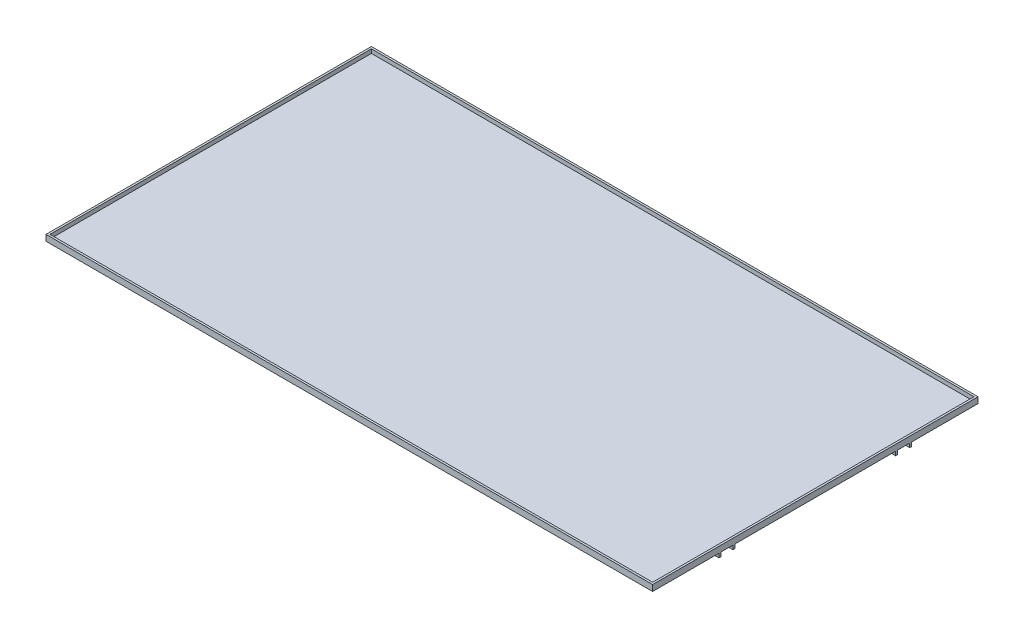
SolidWorks part; units mm, degrees
material "Plain Carbon Steel"
ref_plane "Front Plane" through (0, 0, 0) normal (0, 0, 1) x (1, 0, 0)
ref_plane "Top Plane" through (0, 0, 0) normal (0, 1, 0) x (1, 0, 0)
ref_plane "Right Plane" through (0, 0, 0) normal (1, 0, 0) x (0, 0, -1)
sketch "Sketch2" plane through (0, 0, 0) normal (0, 1, 0) x (1, 0, 0)
  line L1 (-750, 400) -> (750, 400)
  line L2 (-750, 400) -> (-750, -400)
  line L3 (-750, -400) -> (750, -400)
  line L4 (750, 400) -> (750, -400)
  line L5 (-750, 400) -> (750, -400) construction
  line L6 (-750, -400) -> (750, 400) construction
  line L7 (-755, 405) -> (755, 405)
  line L8 (-755, 405) -> (-755, -405)
  line L9 (-755, -405) -> (755, -405)
  line L10 (755, 405) -> (755, -405)
  line L11 (-755, 405) -> (755, -405) construction
  line L12 (-755, -405) -> (755, 405) construction
  point P0 (0, 0)
  point P6 (0, 0)
  dimension "D1" = 1500
  dimension "D2" = 800
  dimension "D3" = 1510
  dimension "D4" = 810
extrude "Boss-Extrude1" add sketch "Sketch2" along normal blind 10
sketch "Sketch3" plane through (0, 0, 0) normal (0, 1, 0) x (1, 0, 0)
  line L0 (-755, 405) -> (-755, -405) construction
  line L1 (755, -405) -> (-755, -405)
  line L2 (755, -405) -> (755, 405)
  line L3 (755, 405) -> (-755, 405)
  line L4 (-755, -405) -> (-755, 405)
  line L5 (755, -405) -> (-755, 405) construction
  line L6 (755, 405) -> (-755, -405) construction
  line L7 (755, 405) -> (-755, 405) construction
  line L8 (-750, 400) -> (-750, -400) construction
  line L9 (730, -380) -> (-730, -380)
  line L10 (730, -380) -> (730, -240)
  line L11 (730, 380) -> (-730, 380)
  line L12 (-730, -380) -> (-730, -240)
  line L13 (730, -380) -> (-730, 380) construction
  line L14 (730, 380) -> (-730, -380) construction
  line L15 (-750, -400) -> (750, -400) construction
  line L16 (-730, -240) -> (730, -240)
  line L17 (-730, -200) -> (-700, -200)
  line L18 (-730, 240) -> (730, 240)
  line L19 (-730, 200) -> (-700, 200)
  line L20 (-730, 240) -> (-730, 380)
  line L21 (-730, -200) -> (-730, 200)
  line L22 (730, -200) -> (730, 200)
  line L23 (730, 240) -> (730, 380)
  line L24 (0, 0) -> (-650, 0) construction
  line L25 (0, 0) -> (650, 0) construction
  line L26 (-500, 240) -> (-500, -240) construction
  line L27 (650, 240) -> (650, -240) construction
  line L28 (-600, 200) -> (600, 200)
  line L30 (-600, 200) -> (-600, -200)
  line L32 (-700, 200) -> (-700, -200)
  line L33 (-600, 200) -> (-700, -200) construction
  line L34 (-600, -200) -> (-700, 200) construction
  line L36 (600, 200) -> (600, -200)
  line L38 (700, 200) -> (700, -200)
  line L39 (600, 200) -> (700, -200) construction
  line L40 (600, -200) -> (700, 200) construction
  line L41 (-600, -200) -> (600, -200)
  line L42 (700, -200) -> (730, -200)
  line L43 (700, 200) -> (730, 200)
  point P0 (0, 0)
  point P10 (0, 0)
  dimension "D1" = 20
  dimension "D2" = 40
  dimension "20" = 20
  dimension "D3" = 40
  dimension "D4" = 200
  dimension "D5" = 200
  dimension "D6" = 650
  dimension "D7" = 650
  dimension "D8" = 100
  dimension "D9" = 100
extrude "Boss-Extrude2" add sketch "Sketch3" against normal blind 5
sketch "Sketch5" plane through (0, -5, 0) normal (0, -1, 0) x (1, 0, 0)
  line L0 (-755, 240) -> (755, 240)
  line L1 (-755, -405) -> (-755, 405) construction
  line L2 (755, 405) -> (755, -405) construction
  line L3 (755, 240) -> (755, 235)
  line L4 (755, 235) -> (-755, 235)
  line L5 (-755, 235) -> (-755, 240)
  dimension "D1" = 5
extrude "Boss-Extrude3" add sketch "Sketch5" along normal blind 10
pattern_linear "LPattern1" count 2 spacing 35 along (0, 0, -1) of "Boss-Extrude3"
pattern_linear "LPattern2" count 2 spacing 440 along (0, 0, -1) of "LPattern1", "Boss-Extrude3"
ref_plane "Plane1" through (0, 0, 220) normal (0, 0, 1) x (1, 0, 0)
sketch "Sketch6" plane through (0, 0, 220) normal (0, 0, 1) x (1, 0, 0)
  line L0 (630, -5) -> (630, -35)
  line L1 (-755, -5) -> (755, -5) construction
  line L3 (670, -35) -> (670, -5)
  line L4 (670, -5) -> (630, -5)
  line L5 (600, -5) -> (600, 0) construction
  arc A0 (670, -35) -> (630, -35) centre (650, -35) cw
  circle A1 centre (650, -35) radius 10
  dimension "D4" = 20
  dimension "D1" = 30
  dimension "D2" = 40
  dimension "30" = 30
extrude "Boss-Extrude4" add sketch "Sketch6" along normal mid plane 10
pattern_linear "LPattern3" count 2 spacing 440 along (0, 0, -1) of "Boss-Extrude4"
sketch "Sketch8" plane through (-755, 0, 0) normal (-1, 0, 0) x (0, 0, 1)
  line L0 (-200, -5) -> (200, -5) construction
  line L1 (-25, -35) -> (-25, -5)
  line L4 (25, -5) -> (25, -35)
  line L5 (-25, -5) -> (25, -5)
  circle A0 centre (0, -35) radius 10
  arc A1 (-25, -35) -> (25, -35) centre (0, -35) ccw
  dimension "D1" = 20
  dimension "D3" = 50
  dimension "D2" = 30
extrude "Boss-Extrude5" add sketch "Sketch8" against normal up to surface (25 mm away) up to face at (-730, -2.5, 0)
sketch "Sketch9" plane through (0, 0, 0) normal (0, 1, 0) x (1, 0, 0)
  line L0 (600, 200) -> (-600, 200) construction
  line L1 (280, 200) -> (200, 200)
  line L2 (280, 200) -> (280, -200)
  line L3 (280, -200) -> (200, -200)
  line L4 (200, 200) -> (200, -200)
  line L5 (-600, -200) -> (600, -200) construction
  line L6 (-600, 200) -> (-600, -200) construction
  dimension "D1" = 800
  dimension "D2" = 80
extrude "Boss-Extrude6" add sketch "Sketch9" against normal up to surface (5 mm away) up to face at (0, -5, -220)
ref_plane "Plane2" through (240, 0, 0) normal (-1, 0, 0) x (0, 0, 1)
sketch "Sketch10" plane through (240, 0, 0) normal (-1, 0, 0) x (0, 0, 1)
  line L2 (25, -5) -> (25, -35)
  line L4 (-25, -35) -> (-25, -5)
  line L5 (-25, -5) -> (25, -5)
  arc A0 (-25, -35) -> (25, -35) centre (0, -35) ccw
  circle A1 centre (0, -35) radius 10
extrude "Boss-Extrude7" add sketch "Sketch10" along normal mid plane 25
sketch "Sketch12" plane through (280, 0, 0) normal (1, 0, 0) x (0, 0, -1)
  line L0 (-200, -5) -> (-200, 0)
  line L1 (-200, 0) -> (200, 0)
  line L2 (200, 0) -> (200, -5)
  line L3 (200, -5) -> (-200, -5)
extrude "Boss-Extrude8" add sketch "Sketch12" along normal blind 100
fillet "Fillet3" radius 10 1 edges at (240, -5, 25)
fillet "Fillet4" radius 10 1 edges at (240, -5, -25)
fillet "Fillet5" radius 10 1 edges at (-742.5, -5, 25)
fillet "Fillet6" radius 10 1 edges at (-742.5, -5, -25)
sketch "Sketch13" plane through (0, -5, 0) normal (0, -1, 0) x (1, 0, 0)
  line L0 (730, -240) -> (730, -380) construction
  line L1 (-730, 380) -> (730, 380)
  line L2 (-730, 380) -> (-730, 240)
  line L3 (-730, 240) -> (730, 240)
  line L4 (730, 380) -> (730, 240)
  line L5 (-730, -380) -> (730, -380)
  line L6 (-730, -380) -> (-730, -240)
  line L7 (-730, -240) -> (730, -240)
  line L8 (730, -380) -> (730, -240)
  line L9 (-700, 200) -> (-700, -200) construction
  line L10 (-600, 200) -> (200, 200)
  line L11 (-600, 200) -> (-600, -200)
  line L12 (-600, -200) -> (200, -200)
  line L13 (200, 200) -> (200, -200)
  line L14 (-730, 200) -> (-700, 200)
  line L15 (-730, 200) -> (-730, -200)
  line L16 (-730, -200) -> (-700, -200)
  line L17 (-700, 200) -> (-700, -200)
  line L18 (600, 200) -> (600, -200) construction
  line L19 (380, 200) -> (600, 200)
  line L20 (380, 200) -> (380, -200)
  line L21 (380, -200) -> (600, -200)
  line L22 (600, 200) -> (600, -200)
  line L23 (730, 200) -> (730, -200) construction
  line L24 (700, 200) -> (730, 200)
  line L25 (700, 200) -> (700, -200)
  line L26 (700, -200) -> (730, -200)
  line L27 (730, 200) -> (730, -200)
extrude "Boss-Extrude9" add sketch "Sketch13" along direction (0, 1, 0) on the side against the normal up to surface (5 mm away)
